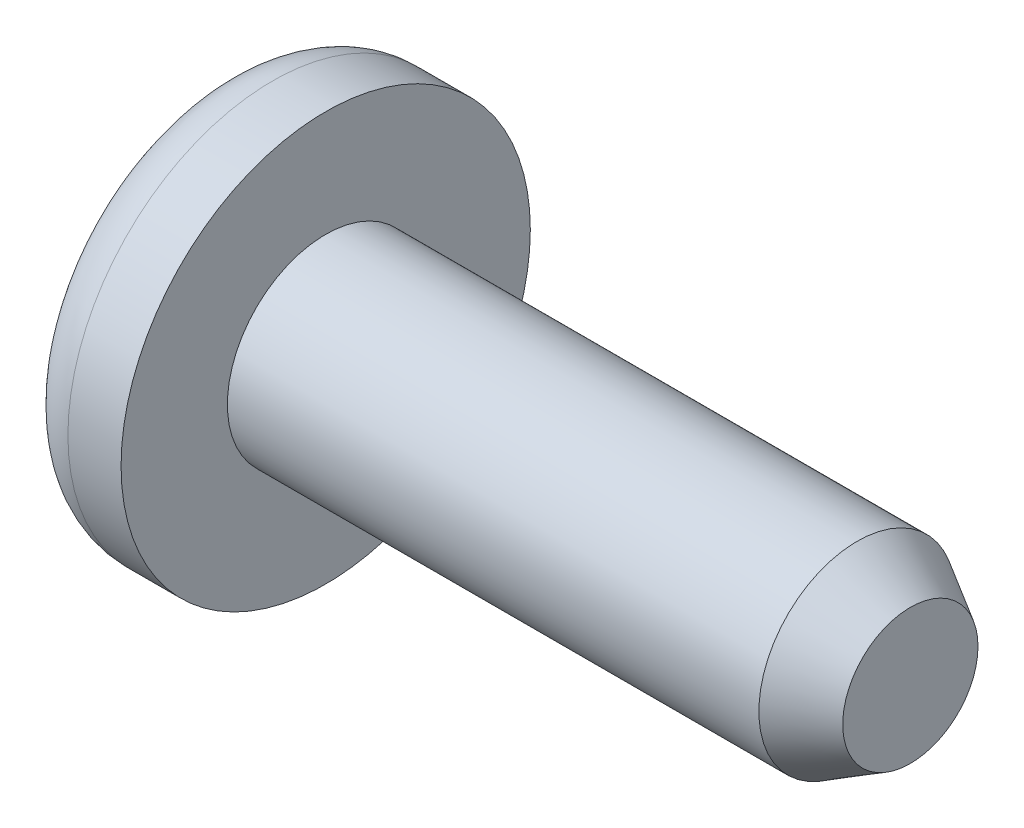
SolidWorks part; units mm, degrees
material "Plain Carbon Steel"
ref_plane "Front Plane" through (0, 0, 0) normal (0, 0, 1) x (1, 0, 0)
ref_plane "Top Plane" through (0, 0, 0) normal (0, 1, 0) x (1, 0, 0)
ref_plane "Right Plane" through (0, 0, 0) normal (1, 0, 0) x (0, 0, -1)
sketch "Sketch1" plane through (0, 0, 0) normal (1, 0, 0) x (0, 0, -1)
  circle A0 centre (0, 0) radius 2.3495
  dimension "D1" = 4.699
extrude "Boss-Extrude1" add sketch "Sketch1" along normal mid plane 13.97
sketch "Sketch2" plane through (0, 0, 0) normal (0, 1, 0) x (1, 0, 0)
  line L5 (-6.985, -2.3495) -> (6.985, -2.3495) construction
  line L6 (-9.525, 0) -> (-6.985, 0)
  line L8 (-9.525, 0) -> (-9.525, -3.6195)
  line L9 (-8.255, -4.8895) -> (-6.985, -4.8895)
  line L10 (-6.985, 0) -> (-6.985, -4.8895)
  line L11 (-6.985, 2.3495) -> (-6.985, -2.3495) construction
  arc A0 (-9.525, -3.6195) -> (-8.255, -4.8895) centre (-8.255, -3.6195) ccw
  point P12 (-9.525, -4.8895)
  dimension "D3" = 1.27
  dimension "D1" = 2.54
  dimension "D2" = 2.54
revolve "Revolve1" add sketch "Sketch2" angle 360 about L6
chamfer "Chamfer1" distance 1.27 angle 30 1 edges at (6.985, 0, -2.3495)
